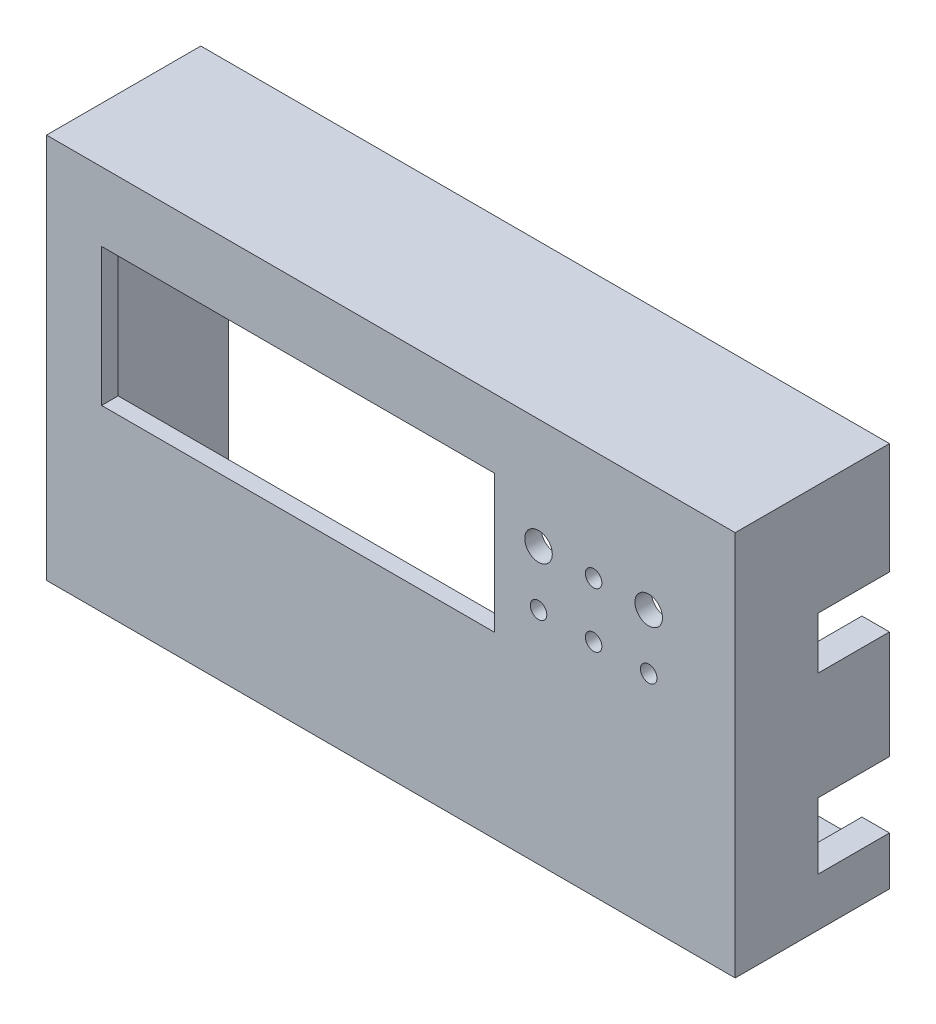
SolidWorks part; units mm, degrees
ref_plane "Front Plane" through (0, 0, 0) normal (0, 0, 1) x (1, 0, 0)
ref_plane "Top Plane" through (0, 0, 0) normal (0, 1, 0) x (1, 0, 0)
ref_plane "Right Plane" through (0, 0, 0) normal (1, 0, 0) x (0, 0, -1)
sketch "Sketch1" plane through (0, 0, 0) normal (0, 0, 1) x (1, 0, 0)
  line L1 (0, 0) -> (125, 0)
  line L2 (0, 0) -> (0, 70)
  line L3 (0, 70) -> (125, 70)
  line L4 (125, 0) -> (125, 70)
  dimension "D1" = 125
  dimension "D2" = 70
extrude "Boss-Extrude1" add sketch "Sketch1" along normal blind 3
sketch "Sketch2" plane through (0, 0, 3) normal (0, 0, 1) x (1, 0, 0)
  line L0 (125, 70) -> (0, 70) construction
  line L1 (10, 57.5) -> (81.3, 57.5)
  line L2 (10, 57.5) -> (10, 32.5)
  line L3 (10, 32.5) -> (81.3, 32.5)
  line L4 (81.3, 57.5) -> (81.3, 32.5)
  line L5 (0, 70) -> (0, 0) construction
  dimension "D1" = 71.3
  dimension "D2" = 25
  dimension "D3" = 12.5
  dimension "D4" = 10
extrude "Cut-Extrude1" cut sketch "Sketch2" against normal blind 5
sketch "Sketch4" plane through (0, 0, 3) normal (0, 0, 1) x (1, 0, 0)
  line L0 (81.3, 32.5) -> (81.3, 57.5) construction
  line L1 (0, 0) -> (125, 0) construction
  circle A0 centre (89.3, 50) radius 2.5
  circle A1 centre (99.3, 50) radius 1.5
  circle A2 centre (109.3, 50) radius 2.5
  circle A3 centre (89.3, 40) radius 1.5
  circle A4 centre (99.3, 40) radius 1.5
  circle A5 centre (109.3, 40) radius 1.5
  dimension "D1" = 5
  dimension "D2" = 3
  dimension "D3" = 5
  dimension "D4" = 3
  dimension "D5" = 3
  dimension "D6" = 3
  dimension "D7" = 8
  dimension "D8" = 10
  dimension "D9" = 10
  dimension "D10" = 8
  dimension "D11" = 10
  dimension "D12" = 10
  dimension "D13" = 40
  dimension "D14" = 40
  dimension "D15" = 50
  dimension "D16" = 50
  dimension "D17" = 50
extrude "Cut-Extrude2" cut sketch "Sketch4" against normal blind 5
sketch "Sketch5" plane through (0, 0, 0) normal (0, 0, -1) x (-1, 0, 0)
  line L0 (-125, 70) -> (0, 70) construction
  line L1 (-5, 5) -> (-120, 5)
  line L2 (-5, 5) -> (-5, 65)
  line L3 (-5, 65) -> (-120, 65)
  line L4 (-120, 5) -> (-120, 65)
  line L5 (-125, 0) -> (-125, 70) construction
  line L6 (0, 70) -> (0, 0) construction
  line L7 (0, 0) -> (-125, 0) construction
  line L9 (0, 0) -> (-125, 0)
  line L10 (0, 0) -> (0, 70)
  line L11 (0, 70) -> (-125, 70)
  line L12 (-125, 0) -> (-125, 70)
  dimension "D1" = 5
  dimension "D2" = 5
  dimension "D3" = 5
  dimension "D4" = 5
extrude "Boss-Extrude2" add sketch "Sketch5" along normal blind 25 contours L9 L12 L11 L10 | L1 L4 L3 L2
sketch "Sketch6" plane through (0, 0, -25) normal (0, 0, -1) x (-1, 0, 0)
  line L0 (0, 70) -> (-125, 70) construction
  line L1 (-125, 0) -> (-125, 70) construction
  line L2 (0, 0) -> (0, 70) construction
  line L3 (0, 0) -> (-125, 0) construction
  circle A0 centre (-122.5, 67.5) radius 2
  circle A1 centre (-2.5, 67.5) radius 2
  circle A2 centre (-2.5, 2.5) radius 2
  circle A3 centre (-122.5, 2.5) radius 2
  dimension "D3" = 4
  dimension "D4" = 2.5
  dimension "D6" = 4
  dimension "D7" = 4
  dimension "D12" = 4
  dimension "D1" = 2.5
  dimension "D2" = 2.5
  dimension "D5" = 2.5
  dimension "D8" = 2.5
  dimension "D9" = 2.5
  dimension "D10" = 2.5
  dimension "D11" = 2.5
extrude "Cut-Extrude3" cut sketch "Sketch6" against normal blind 10
sketch "Sketch7" plane through (125, 0, 0) normal (1, 0, 0) x (0, 0, -1)
  line L0 (25, 0) -> (25, 70) construction
  line L1 (25, 8.8) -> (12, 8.8)
  line L2 (25, 8.8) -> (25, 20.8)
  line L3 (25, 20.8) -> (12, 20.8)
  line L4 (12, 8.8) -> (12, 20.8)
  line L5 (-3, 0) -> (25, 0) construction
  line L6 (25, 40.4) -> (12, 40.4)
  line L7 (25, 40.4) -> (25, 49.8226)
  line L8 (25, 49.8226) -> (12, 49.8226)
  line L9 (12, 40.4) -> (12, 49.8226)
  dimension "D1" = 8.8
  dimension "D2" = 13
  dimension "D3" = 12
  dimension "D4" = 13
  dimension "58" = 40.4
extrude "Cut-Extrude4" cut sketch "Sketch7" against normal blind 10
